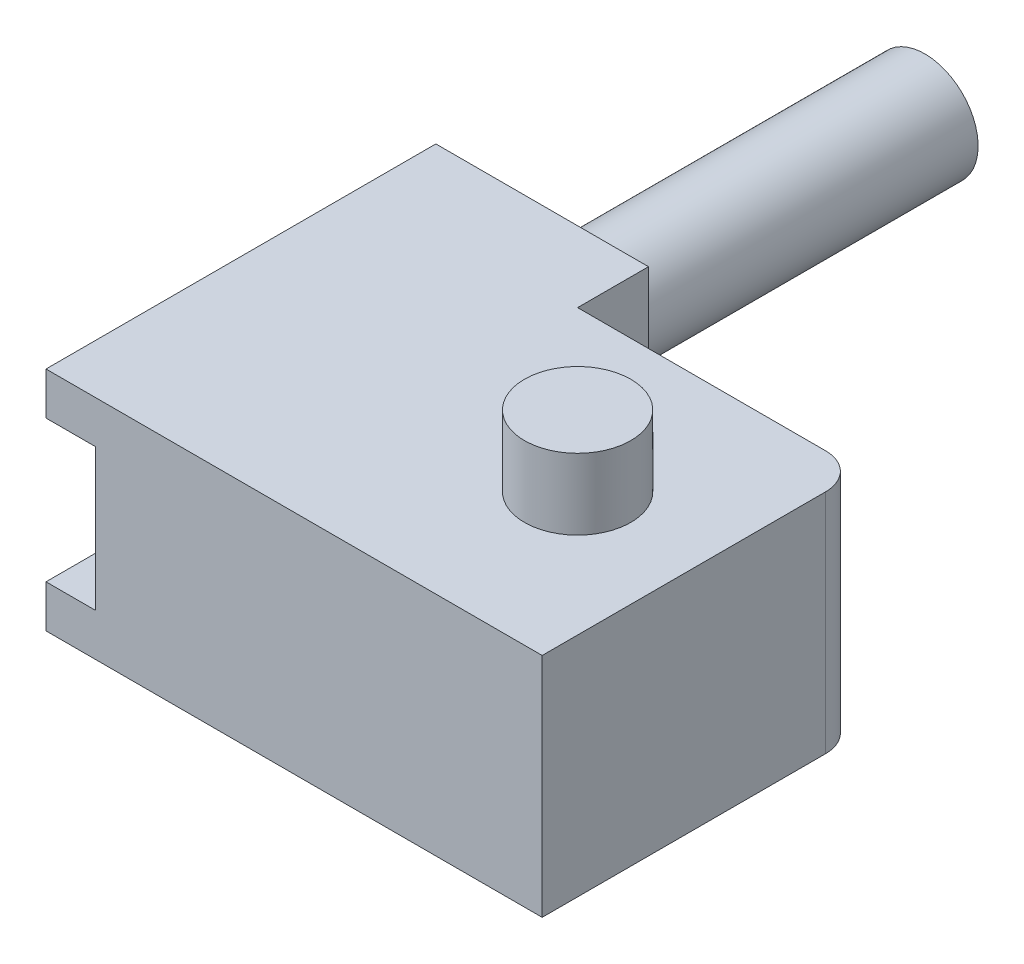
SolidWorks part; units mm, degrees
ref_plane "Alzado" through (0, 0, 0) normal (0, 0, 1) x (1, 0, 0)
ref_plane "Planta" through (0, 0, 0) normal (0, 1, 0) x (1, 0, 0)
ref_plane "Vista lateral" through (0, 0, 0) normal (1, 0, 0) x (0, 0, -1)
sketch "Croquis2" plane through (0, 0, 0) normal (0, 0, 1) x (1, 0, 0)
  line L0 (0, 0) -> (0, 40)
  line L1 (0, 40) -> (70, 40)
  line L2 (70, 40) -> (70, 0)
  line L3 (70, 0) -> (0, 0)
  dimension "D1" = 40
  dimension "D2" = 70
extrude "Saliente-Extruir1" add sketch "Croquis2" along normal blind 45
sketch "Croquis3" plane through (0, 0, 0) normal (0, 0, -1) x (-1, 0, 0)
  line L0 (0, 0) -> (0, 10)
  line L1 (0, 40) -> (0, 0) construction
  line L2 (0, 10) -> (0, 30)
  line L3 (0, 30) -> (0, 40)
  line L4 (0, 10) -> (-70, 10)
  line L5 (-70, 0) -> (-70, 40) construction
  line L6 (-70, 10) -> (-70, 30)
  line L8 (0, 30) -> (-7, 30)
  line L9 (-7, 30) -> (-7, 10)
  line L10 (-7, 10) -> (-47.5, 10)
  line L11 (-7, 10) -> (-7, 30)
  line L12 (-7, 30) -> (-47.5, 30)
  line L13 (-47.5, 10) -> (-47.5, 30)
  dimension "D1" = 10
  dimension "D2" = 10
  dimension "D3" = 7
  dimension "D4" = 40.5
extrude "Cortar-Extruir1" cut sketch "Croquis3" against normal blind 39 contours L13 L4 L9 L12
sketch "Croquis4" plane through (0, 0, 0) normal (0, 0, -1) x (-1, 0, 0)
  line L0 (-7, 10) -> (0, 10)
  line L1 (0, 40) -> (0, 0) construction
  line L2 (0, 10) -> (0, 30)
  line L3 (0, 30) -> (-7, 30)
  line L4 (-7, 30) -> (-7, 10)
  line L6 (-47.5, 10) -> (-54.5, 10)
  line L7 (-47.5, 10) -> (-47.5, 30)
  line L8 (-47.5, 30) -> (-54.5, 30)
  line L9 (-54.5, 10) -> (-54.5, 30)
  dimension "D1" = 7
extrude "Cortar-Extruir2" cut sketch "Croquis4" against normal blind 12 contours L4 L0 L2 L3 | L7 L6 L9 L8
sketch "Croquis5" plane through (0, 0, 0) normal (-1, 0, 0) x (0, 0, 1)
  line L0 (25, 10) -> (25, 30)
  line L1 (25, 10) -> (45, 10)
  line L2 (45, 40) -> (45, 0) construction
  line L3 (45, 10) -> (45, 30)
  line L4 (45, 30) -> (25, 30)
  dimension "D1" = 20
extrude "Cortar-Extruir4" cut sketch "Croquis5" against normal blind 7
sketch "Croquis6" plane through (0, 40, 0) normal (0, 1, 0) x (1, 0, 0)
  line L0 (70, 0) -> (0, 0) construction
  line L1 (70, -45) -> (35, -45) construction
  line L2 (70, -45) -> (70, 0) construction
  line L3 (70, 0) -> (35, 0) construction
  line L4 (35, -45) -> (35, 0) construction
  line L5 (35, 0) -> (70, -45) construction
  circle A0 centre (52.5, -22.5) radius 7.5
  dimension "D1" = 15
  dimension "D2" = 35
extrude "Saliente-Extruir3" add sketch "Croquis6" along normal blind 30
sketch "Croquis8" plane through (0, 0, 0) normal (0, -1, 0) x (1, 0, 0)
  line L0 (0, 0) -> (70, 0) construction
  line L1 (70, 45) -> (35, 45) construction
  line L2 (70, 45) -> (70, 0) construction
  line L3 (70, 0) -> (35, 0) construction
  line L4 (35, 45) -> (35, 0) construction
  line L5 (70, 45) -> (35, 0) construction
  circle A0 centre (52.5, 22.5) radius 7.5
  dimension "D2" = 15
  dimension "D1" = 35
extrude "Saliente-Extruir4" add sketch "Croquis8" along normal blind 30
sketch "Croquis9" plane through (0, 0, 0) normal (0, 0, -1) x (-1, 0, 0)
  line L0 (0, 40) -> (-30, 40)
  line L1 (-70, 40) -> (0, 40) construction
  line L2 (-30, 40) -> (-30, 0)
  line L3 (0, 0) -> (-70, 0) construction
  line L4 (-30, 0) -> (0, 0)
  line L5 (0, 0) -> (0, 40)
  dimension "D1" = 30
extrude "Saliente-Extruir5" add sketch "Croquis9" along normal blind 10
sketch "Croquis10" plane through (0, 0, -10) normal (0, 0, -1) x (-1, 0, 0)
  line L0 (-30, 0) -> (0, 40) construction
  circle A0 centre (-15, 20) radius 7.5
  dimension "D1" = 15
extrude "Saliente-Extruir6" add sketch "Croquis10" along normal blind 54
fillet "Redondeo1" radius 5 1 edges at (70, 20, 0)
sketch "Croquis11" plane through (0, 0, -10) normal (0, 0, -1) x (-1, 0, 0)
  line L0 (0, 0) -> (0, 4)
  line L1 (0, 0) -> (0, 40) construction
  line L2 (0, 4) -> (0, 36)
  line L3 (0, 36) -> (0, 40)
  line L4 (0, 4) -> (-72.2314, 4)
  line L5 (-72.2314, 4) -> (-72.2314, 0)
  line L6 (-72.2314, 0) -> (0, 0)
  line L7 (0, 36) -> (-72.2314, 36)
  line L8 (-72.2314, 36) -> (-72.2314, 40)
  line L9 (-72.2314, 40) -> (0, 40)
  line M7 (0, 0) -> (0, 40)
  line M8 (0, 40) -> (-30, 40)
  line M9 (-30, 40) -> (-30, 0)
  line M10 (-30, 0) -> (0, 0)
  dimension "D1" = 4
  dimension "D2" = 4
extrude "Cortar-Extruir7" cut sketch "Croquis11" against normal blind 60 contours L5 L6 L4 M9 | L9 L8 L7 M9 | L7 M7 M8 M9 | L4 M7 M9 M10
sketch "Croquis12" plane through (0, 70, 0) normal (0, 1, 0) x (1, 0, 0)
  circle A0 centre (52.5, -22.5) radius 7.5
extrude "Saliente-Extruir7" add sketch "Croquis12" against normal blind 100
sketch "Croquis13" plane through (0, 0, -10) normal (0, 0, -1) x (-1, 0, 0)
  line L0 (0, 36) -> (0, 46)
  line L1 (0, 46) -> (0, 86.1293)
  line L2 (0, 86.1293) -> (-75.5499, 86.1293)
  line L3 (-75.5499, 86.1293) -> (-75.5499, 46)
  line L4 (-75.5499, 46) -> (-75.5499, 36)
  line L5 (-75.5499, 36) -> (0, 36)
  line L6 (-75.5499, 46) -> (0, 46)
  line L7 (-75.5499, 4) -> (-75.5499, -6)
  line L9 (-75.5499, -6) -> (0, -6)
  line L10 (-75.5499, 4) -> (0, 4)
  line L11 (-75.5499, -6) -> (-75.5499, 4)
  line L12 (-75.5499, -46.1293) -> (-75.5499, -6)
  line L13 (0, -46.1293) -> (-75.5499, -46.1293)
  line L14 (0, -6) -> (0, -46.1293)
  line L15 (0, 4) -> (0, -6)
  line L16 (0, -6) -> (0, -46.1293)
  line L17 (-75.5499, -46.1293) -> (-75.5499, -6)
  dimension "D1" = 10
extrude "Cortar-Extruir8" cut sketch "Croquis13" against normal blind 100 contours L14 L9 L12 L13 | L3 L6 L1 L2
